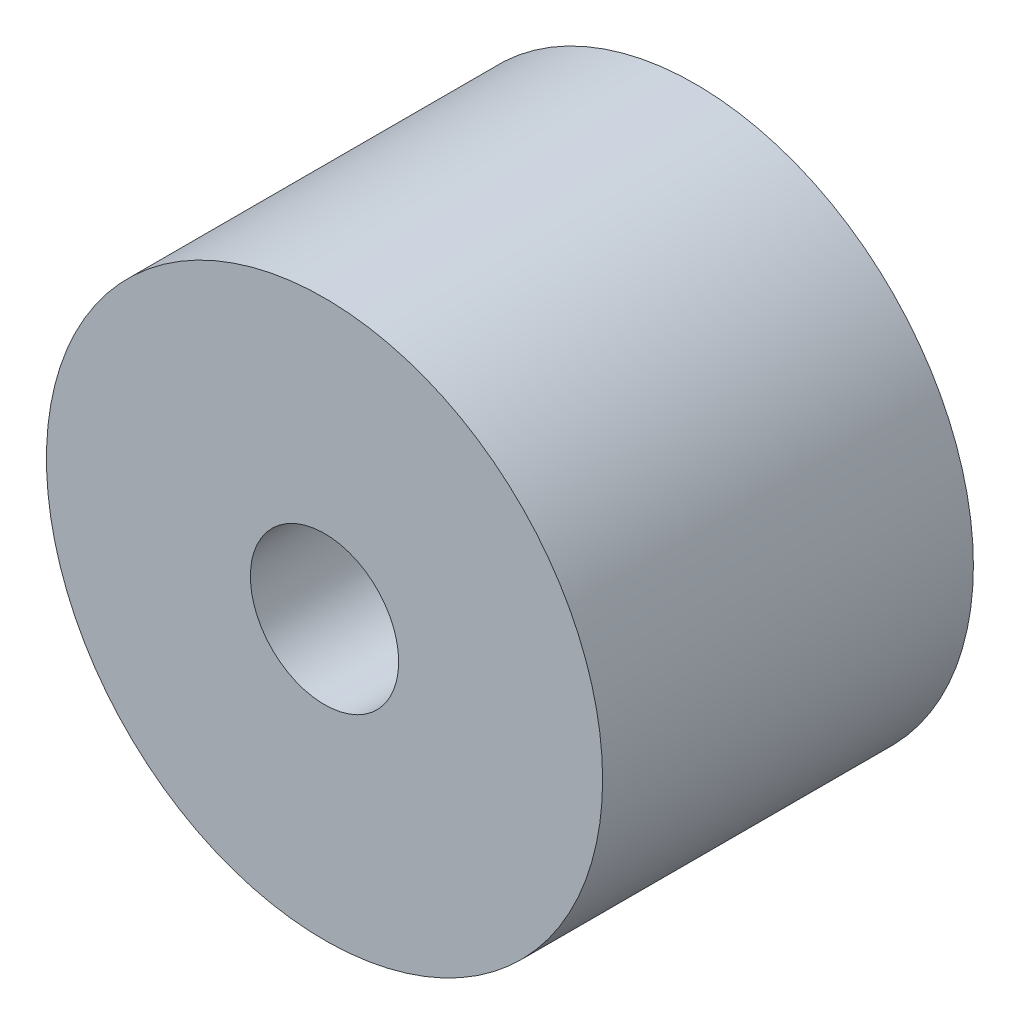
SolidWorks part; units mm, degrees
ref_plane "前视基准面" through (0, 0, 0) normal (0, 0, 1) x (1, 0, 0)
ref_plane "上视基准面" through (0, 0, 0) normal (0, 1, 0) x (1, 0, 0)
ref_plane "右视基准面" through (0, 0, 0) normal (1, 0, 0) x (0, 0, -1)
other "Configuration Table"
sketch "草图1" plane through (0, 0, 0) normal (0, 0, 1) x (1, 0, 0)
  circle A1 centre (0, 0) radius 4
  circle A2 centre (0, 0) radius 15
extrude "凸台-拉伸1" add sketch "草图1" along normal mid plane 20
